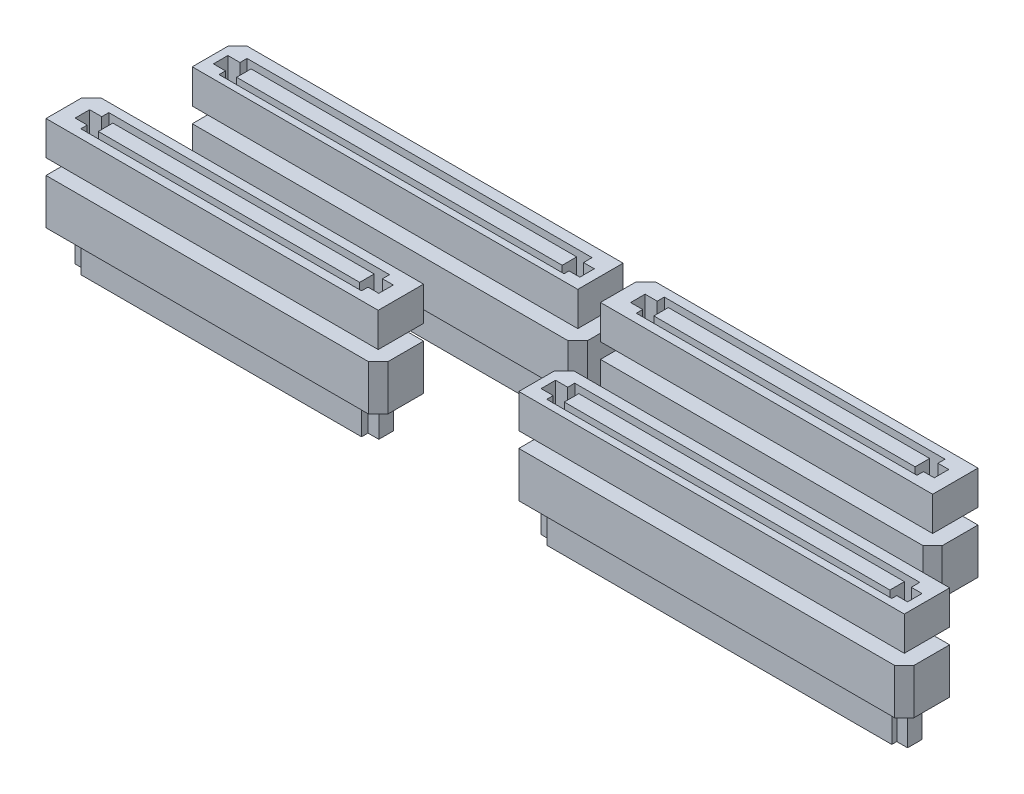
SolidWorks part; units mm, degrees
ref_plane "Front Plane" through (0, 0, 0) normal (0, 0, 1) x (1, 0, 0)
ref_plane "Top Plane" through (0, 0, 0) normal (0, 1, 0) x (1, 0, 0)
ref_plane "Right Plane" through (0, 0, 0) normal (1, 0, 0) x (0, 0, -1)
ref_plane "Plane1" through (0, -1.6866, 0) normal (0, 1, 0) x (1, 0, 0)
ref_plane "center-of-slot" through (0, -0.8433, 0) normal (0, 1, 0) x (1, 0, 0)
sketch "Sketch1" plane through (0, 0, 0) normal (0, 1, 0) x (1, 0, 0)
  line L0 (55.811, 9.5) -> (97.25, 9.5)
  line L1 (3.686, 9.5) -> (39.25, 9.5)
  line L2 (2.625, 8.439) -> (2.625, 4.5)
  line L3 (2.625, 4.5) -> (39.25, 4.5) construction
  line L4 (39.25, 9.5) -> (39.25, 4.5) construction
  line L5 (0, 0) -> (100, 0) construction
  line L6 (0, 0) -> (0, 75) construction
  line L7 (0, 75) -> (100, 75) construction
  line L8 (100, 0) -> (100, 75) construction
  line L9 (54.75, 8.439) -> (54.75, 4.5)
  line L10 (54.75, 4.5) -> (97.25, 4.5) construction
  line L11 (97.25, 9.5) -> (97.25, 4.5) construction
  line L12 (51.811, 22.5) -> (87.375, 22.5)
  line L13 (6.811, 22.5) -> (48.25, 22.5)
  line L14 (5.75, 21.439) -> (5.75, 17.5)
  line L15 (5.75, 17.5) -> (48.25, 17.5) construction
  line L16 (48.25, 22.5) -> (48.25, 17.5) construction
  line L17 (50.75, 21.439) -> (50.75, 17.5)
  line L18 (50.75, 17.5) -> (87.375, 17.5) construction
  line L19 (87.375, 22.5) -> (87.375, 17.5) construction
  line L20 (5.75, 21.439) -> (6.811, 22.5)
  line L21 (50.75, 21.439) -> (51.811, 22.5)
  line L22 (54.75, 8.439) -> (55.811, 9.5)
  line L23 (2.625, 8.439) -> (3.686, 9.5)
  line L24 (2.625, 4.5) -> (38.195, 4.5)
  line L25 (38.195, 4.5) -> (39.25, 5.555) construction
  line L26 (39.25, 5.555) -> (39.25, 9.5)
  line L27 (50.75, 17.5) -> (86.32, 17.5)
  line L28 (86.32, 17.5) -> (87.375, 18.555) construction
  line L29 (87.375, 18.555) -> (87.375, 22.5)
  line L30 (54.75, 4.5) -> (96.19, 4.5)
  line L31 (96.19, 4.5) -> (97.25, 5.56) construction
  line L32 (97.25, 5.56) -> (97.25, 9.5)
  line L33 (5.75, 17.5) -> (47.19, 17.5)
  line L34 (47.19, 17.5) -> (48.25, 18.56) construction
  line L35 (48.25, 18.56) -> (48.25, 22.5)
  line L36 (47.19, 17.5) -> (48.25, 17.5)
  line L37 (48.25, 17.5) -> (48.25, 18.56)
  line L38 (38.195, 4.5) -> (39.25, 4.5)
  line L39 (39.25, 4.5) -> (39.25, 5.555)
  line L40 (86.32, 17.5) -> (87.375, 17.5)
  line L41 (87.375, 17.5) -> (87.375, 18.555)
  line L42 (96.19, 4.5) -> (97.25, 4.5)
  line L43 (97.25, 4.5) -> (97.25, 5.56)
  point P0 (2.625, 9.5)
  point P9 (54.75, 9.5)
  point P13 (5.75, 22.5)
  point P17 (50.75, 22.5)
extrude "SV" add sketch "Sketch1" along normal blind 3.75
sketch "Sketch3" plane through (0, 3.75, 0) normal (0, 1, 0) x (1, 0, 0)
  line L0 (4.1893, 7.7457) -> (5.5243, 7.7457)
  line L1 (4.1893, 8.5242) -> (37.667, 8.5242) construction
  line L2 (4.1893, 8.5242) -> (4.1893, 5.4386) construction
  line L3 (4.1893, 5.4386) -> (37.667, 5.4386) construction
  line L4 (37.667, 8.5242) -> (37.667, 5.4386) construction
  line L5 (5.5243, 7.7457) -> (5.5243, 8.5242)
  line L6 (5.5243, 8.5242) -> (36.4757, 8.5242)
  line L7 (36.4757, 8.5242) -> (36.4757, 7.7457)
  line L8 (36.4757, 7.7457) -> (37.667, 7.7457)
  line L9 (37.667, 7.7457) -> (37.667, 6.1479)
  line L10 (37.667, 6.1479) -> (36.4757, 6.1479)
  line L11 (36.4757, 6.1479) -> (36.4757, 5.4386)
  line L12 (36.4757, 5.4386) -> (5.5243, 5.4386)
  line L13 (5.5243, 5.4386) -> (5.5243, 6.1479)
  line L14 (5.5243, 6.1479) -> (4.1893, 6.1479)
  line L15 (4.1893, 6.1479) -> (4.1893, 7.7457)
  line L16 (52.4211, 20.7536) -> (53.7561, 20.7536)
  line L17 (6.7471, 7.7457) -> (35.5588, 7.7457)
  line L18 (6.7471, 7.7457) -> (6.7471, 6.1479)
  line L19 (6.7471, 6.1479) -> (35.5588, 6.1479)
  line L20 (35.5588, 7.7457) -> (35.5588, 6.1479)
  line L21 (52.4211, 21.532) -> (85.8988, 21.532) construction
  line L22 (52.4211, 21.532) -> (52.4211, 18.4464) construction
  line L23 (52.4211, 18.4464) -> (85.8988, 18.4464) construction
  line L24 (85.8988, 21.532) -> (85.8988, 18.4464) construction
  line L25 (53.7561, 20.7536) -> (53.7561, 21.532)
  line L26 (53.7561, 21.532) -> (84.7075, 21.532)
  line L27 (84.7075, 21.532) -> (84.7075, 20.7536)
  line L28 (84.7075, 20.7536) -> (85.8988, 20.7536)
  line L29 (85.8988, 20.7536) -> (85.8988, 19.1558)
  line L30 (85.8988, 19.1558) -> (84.7075, 19.1558)
  line L31 (84.7075, 19.1558) -> (84.7075, 18.4464)
  line L32 (84.7075, 18.4464) -> (53.7561, 18.4464)
  line L33 (53.7561, 18.4464) -> (53.7561, 19.1558)
  line L34 (53.7561, 19.1558) -> (52.4211, 19.1558)
  line L35 (52.4211, 19.1558) -> (52.4211, 20.7536)
  line L36 (54.9789, 20.7536) -> (83.7906, 20.7536)
  line L37 (54.9789, 20.7536) -> (54.9789, 19.1558)
  line L38 (54.9789, 19.1558) -> (83.7906, 19.1558)
  line L39 (83.7906, 20.7536) -> (83.7906, 19.1558)
  line L40 (55.7059, 7.599) -> (57.0409, 7.599)
  line L41 (55.7059, 8.3775) -> (96.2696, 8.3775) construction
  line L42 (55.7059, 8.3775) -> (55.7059, 5.2919) construction
  line L43 (55.7059, 5.2919) -> (96.2696, 5.2919) construction
  line L44 (96.2696, 8.3775) -> (96.2696, 5.2919) construction
  line L45 (57.0409, 7.599) -> (57.0409, 8.3775)
  line L46 (57.0409, 8.3775) -> (95.0783, 8.3775)
  line L47 (95.0783, 8.3775) -> (95.0783, 7.4377)
  line L48 (95.0783, 7.4377) -> (96.2696, 7.4377)
  line L49 (96.2696, 7.4377) -> (96.2696, 5.8399)
  line L50 (96.2696, 5.8399) -> (95.0783, 5.8399)
  line L51 (95.0783, 5.8399) -> (95.0783, 5.2919)
  line L52 (95.0783, 5.2919) -> (57.0409, 5.2919)
  line L53 (57.0409, 5.2919) -> (57.0409, 6.0012)
  line L54 (57.0409, 6.0012) -> (55.7059, 6.0012)
  line L55 (55.7059, 6.0012) -> (55.7059, 7.599)
  line L56 (58.2637, 7.599) -> (94.1615, 7.599)
  line L57 (58.2637, 7.599) -> (58.2637, 6.0012)
  line L58 (58.2637, 6.0012) -> (94.1615, 6.0012)
  line L59 (94.1615, 7.599) -> (94.1615, 6.0012)
  line L60 (6.6366, 20.5397) -> (7.9716, 20.5397)
  line L61 (6.6366, 21.3182) -> (47.2003, 21.3182) construction
  line L62 (6.6366, 21.3182) -> (6.6366, 18.2325) construction
  line L63 (6.6366, 18.2325) -> (47.2003, 18.2325) construction
  line L64 (47.2003, 21.3182) -> (47.2003, 18.2325) construction
  line L65 (7.9716, 20.5397) -> (7.9716, 21.3182)
  line L66 (7.9716, 21.3182) -> (46.009, 21.3182)
  line L67 (46.009, 21.3182) -> (46.009, 20.3784)
  line L68 (46.009, 20.3784) -> (47.2003, 20.3784)
  line L69 (47.2003, 20.3784) -> (47.2003, 18.7806)
  line L70 (47.2003, 18.7806) -> (46.009, 18.7806)
  line L71 (46.009, 18.7806) -> (46.009, 18.2325)
  line L72 (46.009, 18.2325) -> (7.9716, 18.2325)
  line L73 (7.9716, 18.2325) -> (7.9716, 18.9419)
  line L74 (7.9716, 18.9419) -> (6.6366, 18.9419)
  line L75 (6.6366, 18.9419) -> (6.6366, 20.5397)
  line L76 (9.1944, 20.5397) -> (45.0922, 20.5397)
  line L77 (9.1944, 20.5397) -> (9.1944, 18.9419)
  line L78 (9.1944, 18.9419) -> (45.0922, 18.9419)
  line L79 (45.0922, 20.5397) -> (45.0922, 18.9419)
extrude "Cut-Extrude1" cut sketch "Sketch3" against normal blind 3.5
sketch "Sketch6" plane through (0, -1.6866, 0) normal (0, 1, 0) x (1, 0, 0)
  line L0 (2.625, 4.5) -> (2.625, 9.5) construction
  line L1 (5.75, 22.5) -> (48.25, 22.5) construction
  line L2 (5.75, 22.5) -> (5.75, 17.5) construction
  line L3 (5.75, 17.5) -> (48.25, 17.5) construction
  line L4 (48.25, 22.5) -> (48.25, 17.5) construction
  line L5 (50.75, 22.5) -> (87.375, 22.5) construction
  line L6 (50.75, 22.5) -> (50.75, 17.5) construction
  line L7 (50.75, 17.5) -> (87.375, 17.5) construction
  line L8 (87.375, 22.5) -> (87.375, 17.5) construction
  line L9 (97.25, 9.5) -> (54.75, 9.5) construction
  line L10 (97.25, 9.5) -> (97.25, 4.5) construction
  line L11 (97.25, 4.5) -> (54.75, 4.5) construction
  line L12 (54.75, 9.5) -> (54.75, 4.5) construction
  line L13 (39.25, 9.5) -> (2.625, 9.5) construction
  line L14 (39.25, 9.5) -> (39.25, 4.5) construction
  line L15 (39.25, 4.5) -> (2.625, 4.5) construction
  line L16 (2.625, 9.5) -> (2.625, 4.5) construction
  line L17 (2.625, 4.5) -> (38.195, 4.5)
  line L18 (2.625, 9.5) -> (39.25, 9.5) construction
  line L19 (48.25, 18.5619) -> (47.1881, 17.5)
  line L20 (39.25, 5.555) -> (39.25, 9.5)
  line L21 (48.25, 18.5619) -> (48.25, 22.5)
  line L22 (47.1881, 17.5) -> (5.75, 17.5)
  line L23 (39.25, 5.555) -> (38.195, 4.5)
  line L24 (54.75, 4.5) -> (96.19, 4.5)
  line L25 (96.19, 4.5) -> (97.25, 5.56)
  line L26 (97.25, 5.56) -> (97.25, 9.5)
  line L27 (50.75, 17.5) -> (86.32, 17.5)
  line L28 (86.32, 17.5) -> (87.375, 18.555)
  line L29 (87.375, 18.555) -> (87.375, 22.5)
  line L30 (2.625, 4.5) -> (2.625, 8.44)
  line L31 (2.625, 8.44) -> (3.685, 9.5) construction
  line L32 (3.685, 9.5) -> (39.25, 9.5)
  line L33 (5.75, 17.5) -> (5.75, 21.44)
  line L34 (5.75, 21.44) -> (6.81, 22.5) construction
  line L35 (6.81, 22.5) -> (48.25, 22.5)
  line L36 (54.75, 4.5) -> (54.75, 8.44)
  line L37 (54.75, 8.44) -> (55.81, 9.5) construction
  line L38 (55.81, 9.5) -> (97.25, 9.5)
  line L39 (87.375, 22.5) -> (51.805, 22.5)
  line L40 (51.805, 22.5) -> (50.75, 21.445) construction
  line L41 (50.75, 21.445) -> (50.75, 17.5)
  line L42 (3.685, 9.5) -> (2.625, 9.5)
  line L43 (2.625, 9.5) -> (2.625, 8.44)
  line L44 (6.81, 22.5) -> (5.75, 22.5)
  line L45 (5.75, 22.5) -> (5.75, 21.44)
  line L46 (50.75, 21.445) -> (50.75, 22.5)
  line L47 (50.75, 22.5) -> (51.805, 22.5)
  line L48 (54.75, 8.44) -> (54.75, 9.5)
  line L49 (54.75, 9.5) -> (55.81, 9.5)
  point P0 (5.75, 22.5)
  point P6 (50.75, 22.5)
  point P15 (54.75, 9.5)
extrude "SV4(a)" add sketch "Sketch6" against normal blind 5 separate body
sketch "Sketch7" plane through (0, -6.6866, 0) normal (0, -1, 0) x (1, 0, 0)
  line L0 (7.9716, -21.3182) -> (7.9716, -20.5397)
  line L1 (7.9716, -20.5397) -> (6.6366, -20.5397)
  line L2 (6.6366, -20.5397) -> (6.6366, -18.9419)
  line L3 (6.6366, -18.9419) -> (7.9716, -18.9419)
  line L4 (7.9716, -18.9419) -> (7.9716, -18.2325)
  line L6 (7.9716, -18.2325) -> (46.009, -18.2325)
  line L7 (46.009, -18.2325) -> (46.009, -18.7806)
  line L8 (46.009, -18.7806) -> (47.2003, -18.7806)
  line L9 (47.2003, -18.7806) -> (47.2003, -20.3784)
  line L10 (47.2003, -20.3784) -> (46.009, -20.3784)
  line L11 (46.009, -20.3784) -> (46.009, -21.3182)
  line L12 (46.009, -21.3182) -> (7.9716, -21.3182)
  line L13 (53.7561, -21.532) -> (84.7075, -21.532)
  line L14 (9.1944, -20.5397) -> (45.0922, -20.5397)
  line L15 (9.1944, -20.5397) -> (9.1944, -18.9419)
  line L16 (9.1944, -18.9419) -> (45.0922, -18.9419)
  line L17 (45.0922, -20.5397) -> (45.0922, -18.9419)
  line L18 (54.9789, -20.7536) -> (83.7906, -20.7536)
  line L19 (54.9789, -20.7536) -> (54.9789, -19.1558)
  line L20 (54.9789, -19.1558) -> (83.7906, -19.1558)
  line L21 (83.7906, -20.7536) -> (83.7906, -19.1558)
  line L22 (94.1615, -7.599) -> (58.2637, -7.599)
  line L23 (94.1615, -7.599) -> (94.1615, -6.0012)
  line L24 (94.1615, -6.0012) -> (58.2637, -6.0012)
  line L25 (58.2637, -7.599) -> (58.2637, -6.0012)
  line L26 (35.5588, -7.7457) -> (6.7471, -7.7457)
  line L27 (35.5588, -7.7457) -> (35.5588, -6.1479)
  line L28 (35.5588, -6.1479) -> (6.7471, -6.1479)
  line L29 (6.7471, -7.7457) -> (6.7471, -6.1479)
  line L30 (84.7075, -21.532) -> (84.7075, -20.7536)
  line L31 (84.7075, -20.7536) -> (85.8988, -20.7536)
  line L32 (85.8988, -20.7536) -> (85.8988, -19.1558)
  line L33 (85.8988, -19.1558) -> (84.7075, -19.1558)
  line L34 (84.7075, -19.1558) -> (84.7075, -18.4464)
  line L35 (84.7075, -18.4464) -> (53.7561, -18.4464)
  line L36 (53.7561, -18.4464) -> (53.7561, -19.1558)
  line L37 (53.7561, -19.1558) -> (52.4211, -19.1558)
  line L38 (52.4211, -19.1558) -> (52.4211, -20.7536)
  line L39 (52.4211, -20.7536) -> (53.7561, -20.7536)
  line L40 (53.7561, -20.7536) -> (53.7561, -21.532)
  line L41 (57.0409, -8.3775) -> (57.0409, -7.599)
  line L42 (57.0409, -7.599) -> (55.7059, -7.599)
  line L43 (55.7059, -7.599) -> (55.7059, -6.0012)
  line L44 (55.7059, -6.0012) -> (57.0409, -6.0012)
  line L45 (57.0409, -6.0012) -> (57.0409, -5.2919)
  line L46 (57.0409, -5.2919) -> (95.0783, -5.2919)
  line L47 (95.0783, -5.2919) -> (95.0783, -5.8399)
  line L48 (95.0783, -5.8399) -> (96.2696, -5.8399)
  line L49 (96.2696, -5.8399) -> (96.2696, -7.4377)
  line L50 (96.2696, -7.4377) -> (95.0783, -7.4377)
  line L51 (95.0783, -7.4377) -> (95.0783, -8.3775)
  line L52 (95.0783, -8.3775) -> (57.0409, -8.3775)
  line L53 (4.1893, -6.1479) -> (5.5243, -6.1479)
  line L54 (5.5243, -6.1479) -> (5.5243, -5.4386)
  line L55 (5.5243, -5.4386) -> (36.4757, -5.4386)
  line L56 (36.4757, -5.4386) -> (36.4757, -6.1479)
  line L57 (36.4757, -6.1479) -> (37.667, -6.1479)
  line L58 (37.667, -6.1479) -> (37.667, -7.7457)
  line L59 (37.667, -7.7457) -> (36.4757, -7.7457)
  line L60 (36.4757, -7.7457) -> (36.4757, -8.5242)
  line L61 (36.4757, -8.5242) -> (5.5243, -8.5242)
  line L62 (5.5243, -8.5242) -> (5.5243, -7.7457)
  line L63 (5.5243, -7.7457) -> (4.1893, -7.7457)
  line L64 (4.1893, -7.7457) -> (4.1893, -6.1479)
extrude "SV4(b)" add sketch "Sketch7" along normal blind 3.5
